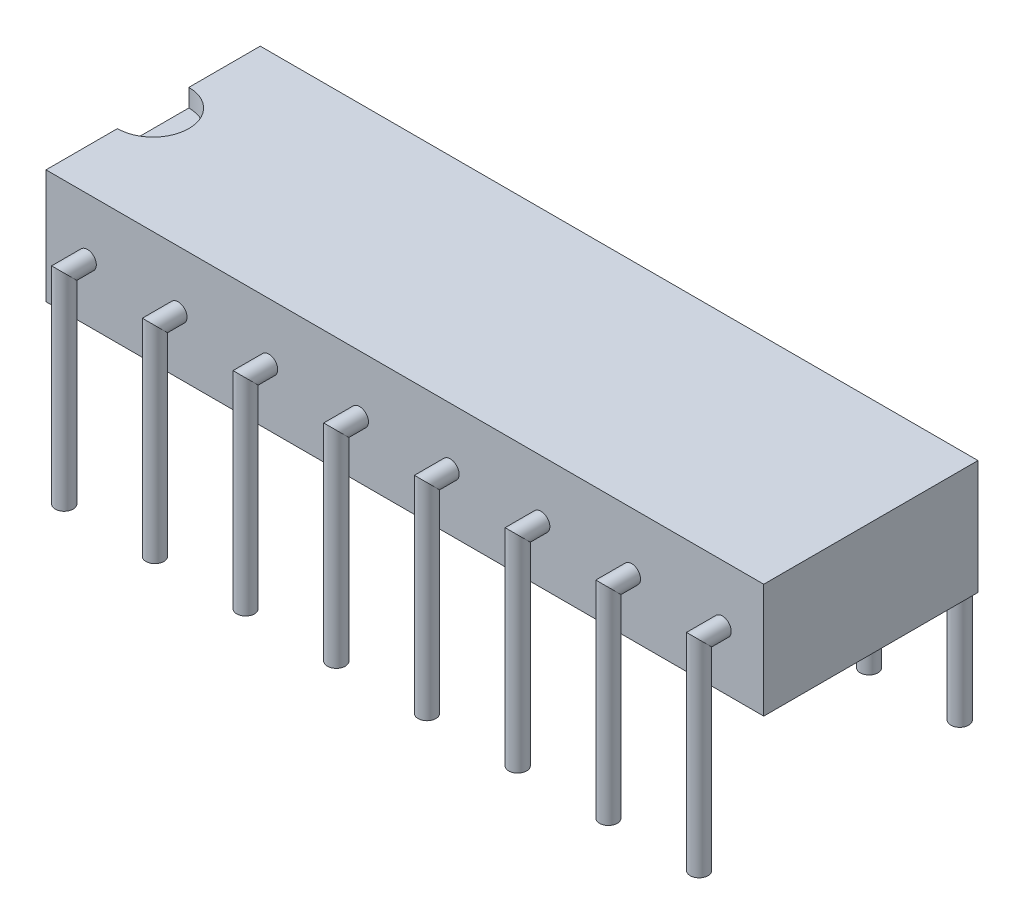
SolidWorks part; units mm, degrees
ref_plane "Plan de face" through (0, 0, 0) normal (0, 0, 1) x (1, 0, 0)
ref_plane "Plan de dessus" through (0, 0, 0) normal (0, 1, 0) x (1, 0, 0)
ref_plane "Plan de droite" through (0, 0, 0) normal (1, 0, 0) x (0, 0, -1)
sketch "Esquisse1" plane through (0, 0, 0) normal (1, 0, 0) x (0, 0, -1)
  line L0 (-34.0084, 0) -> (28.7946, 0) construction
  line L1 (0, -15.76) -> (0, 25.9507) construction
  line L2 (-13.1897, 3.2) -> (13.1184, 3.2) construction
  line L3 (3, 10.112) -> (3, -6.1718) construction
  line L4 (-3, 10.112) -> (-3, -4.99) construction
  line L6 (-3, 3.2) -> (3, 3.2)
  line L7 (-3, 3.2) -> (-3, 0)
  line L8 (-3, 0) -> (3, 0)
  line L9 (3, 3.2) -> (3, 0)
  dimension "D1" = 3
  dimension "D2" = 6
  dimension "D3" = 3.2
extrude "Extrusion1" add sketch "Esquisse1" along normal blind 20.1
sketch "Esquisse2" plane through (0, 3.2, 0) normal (0, 1, 0) x (-1, 0, 0)
  line L0 (0, -1) -> (0, 1)
  arc A0 (0, 1) -> (0, -1) centre (0, 0) ccw
extrude "Enlèv. mat.-Extru.1" cut sketch "Esquisse2" against normal blind 0.5
sketch "Esquisse3" plane through (0, 0, 3) normal (0, 0, 1) x (1, 0, 0)
  line L0 (-0.9705, 0) -> (10.7632, 0) construction
  line L1 (0, 4.319) -> (0, -1.0907) construction
  line L2 (-0.7349, 1.6) -> (2.3847, 1.6) construction
  line L3 (1.16, 2.698) -> (1.16, -1.0907) construction
  circle A0 centre (1.16, 1.6) radius 0.25
  dimension "D1" = 1.6
  dimension "D2" = 1.16
ref_plane "Plan1" through (1.16, 0, 0) normal (1, 0, 0) x (0, 0, -1)
sketch "Esquisse5" plane through (1.16, 0, 0) normal (1, 0, 0) x (0, 0, -1)
  line L0 (-4.2866, 0) -> (4.976, 0) construction
  line L1 (-3, -1.7147) -> (-3, 5.2592) construction
  line L2 (-4.2866, -4) -> (4.976, -4) construction
  line L3 (-3.65, -4.4343) -> (-3.65, 4.8284) construction
  line L4 (-3.7349, 1.6) -> (-3, 1.6) construction
  line L5 (-3, 1.6) -> (-3.65, 1.6)
  line L6 (-3.65, 1.6) -> (-3.65, -4)
  dimension "D1" = 4
  dimension "D2" = 0.65
sweep "Balayage1" add profiles "Esquisse3" path "Esquisse5"
ref_plane "Plan2" through (0, 0, 0) normal (0, 0, 1) x (1, 0, 0)
mirror "Symétrie1" about plane through (0, 0, 0) normal (0, 0, 1) of "Balayage1"
pattern_linear "Répétition linéaire1" count 8 spacing 2.54 along (1, 0, 0) of "Balayage1", "Symétrie1"
